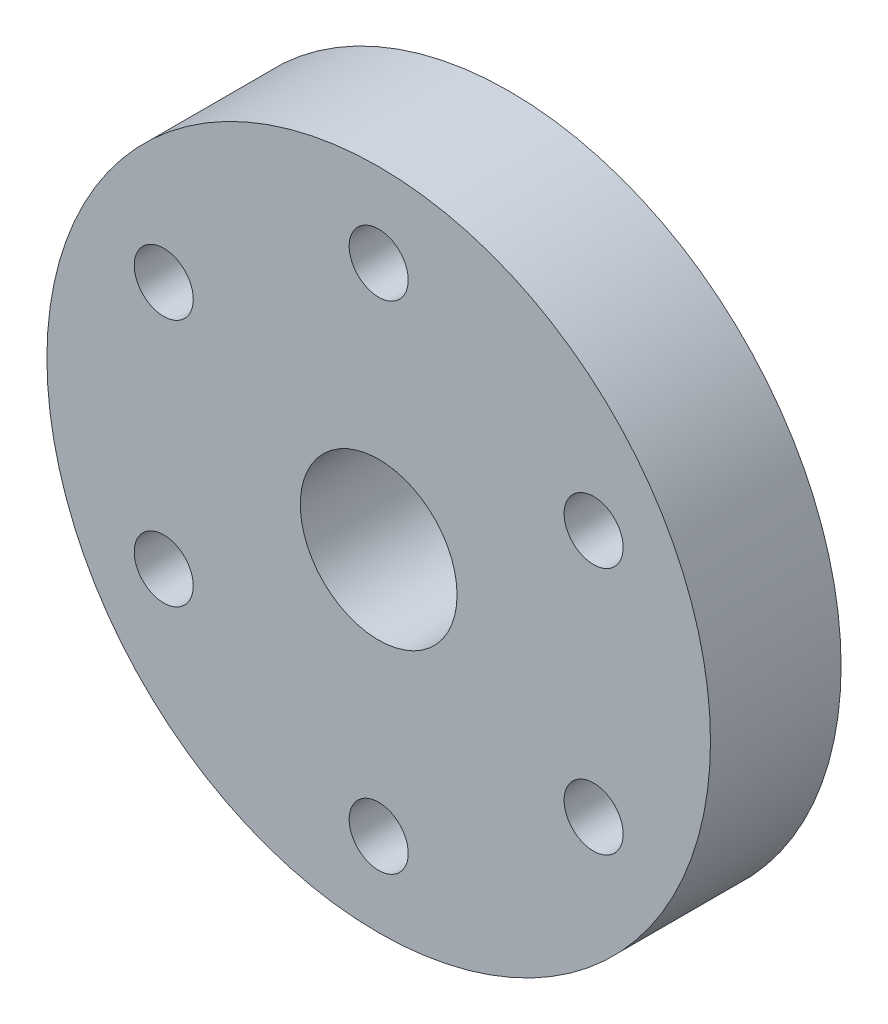
SolidWorks part; units mm, degrees
material "1060 Alloy"
ref_plane "Front Plane" through (0, 0, 0) normal (0, 0, 1) x (1, 0, 0)
ref_plane "Top Plane" through (0, 0, 0) normal (0, 1, 0) x (1, 0, 0)
ref_plane "Right Plane" through (0, 0, 0) normal (1, 0, 0) x (0, 0, -1)
sketch "Sketch1" plane through (0, 0, 0) normal (0, 0, 1) x (1, 0, 0)
  circle A0 centre (0, 0) radius 6
  circle A1 centre (0, 0) radius 3
  dimension "D1" = 12
  dimension "D2" = 6
extrude "Boss-Extrude1" add sketch "Sketch1" along normal blind 4.2
sketch "Sketch2" plane through (0, 0, 4.2) normal (0, 0, 1) x (1, 0, 0)
  circle A0 centre (0, 0) radius 12.7
  circle A1 centre (0, 0) radius 3
  dimension "D1" = 25.4
extrude "Boss-Extrude2" add sketch "Sketch2" along normal blind 5
sketch "Sketch3" plane through (0, 0, 0) normal (0, 1, 0) x (1, 0, 0)
  line L0 (0, 0) -> (0, -2.1) construction
  circle A0 centre (0, -2.1) radius 1.4
  dimension "D2" = 2.8
  dimension "D1" = 2.1
extrude "Cut-Extrude1" cut sketch "Sketch3" against normal through all
sketch "Sketch4" plane through (0, 0, 9.2) normal (0, 0, 1) x (1, 0, 0)
  circle A1 centre (0, 9.5) radius 1.4
  circle A2 centre (8.2272, 4.75) radius 1.4
  circle A3 centre (8.2272, -4.75) radius 1.4
  circle A4 centre (0, -9.5) radius 1.4
  circle A5 centre (-8.2272, -4.75) radius 1.4
  circle A6 centre (-8.2272, 4.75) radius 1.4
  point P18 (0, 0)
  dimension "D2" = 2.8
  dimension "D3" = 6
hole_wizard "#4-40 Tapped Hole1" positions "Sketch6" profile "Sketch5" tap size "#4-40" standard "ANSI Inch"
sketch "Sketch6" plane through (0, 0, 9.2) normal (0, 0, 1) x (1, 0, 0)
  point P0 (-8.2272, -4.75)
  point P3 (-8.2272, 4.75)
  point P6 (0, 9.5)
  point P9 (8.2272, 4.75)
  point P12 (8.2272, -4.75)
  point P15 (0, -9.5)
sketch "Sketch5" plane through (-8.2272, -4.75, 9.2) normal (1, 0, 0) x (0, -1, 0)
  line L0 (0, 0) -> (0, 8.2792)
  line L1 (0, 8.2792) -> (1.1303, 7.6)
  line L2 (1.1303, 7.6) -> (1.1303, 0)
  line L5 (1.1303, 0) -> (0, 0)
  line L10 (0, 8.2792) -> (-1.1303, 7.6) construction
  line L11 (0, -6.35) -> (0, 107.95) construction
  dimension "Tap Drill Dia." = 2.2606
  dimension "Tap Drill Depth" = 7.6
  dimension "Drill Angle" = 118
cosmetic thread "Hole Thread1" parameters "D1"=5, "D2"=2.8448
cosmetic thread "Hole Thread2" parameters "D1"=5, "D2"=2.8448
cosmetic thread "Hole Thread3" parameters "D1"=5, "D2"=2.8448
cosmetic thread "Hole Thread4" parameters "D1"=5, "D2"=2.8448
cosmetic thread "Hole Thread5" parameters "D1"=5, "D2"=2.8448
cosmetic thread "Hole Thread6" parameters "D1"=5, "D2"=2.8448
